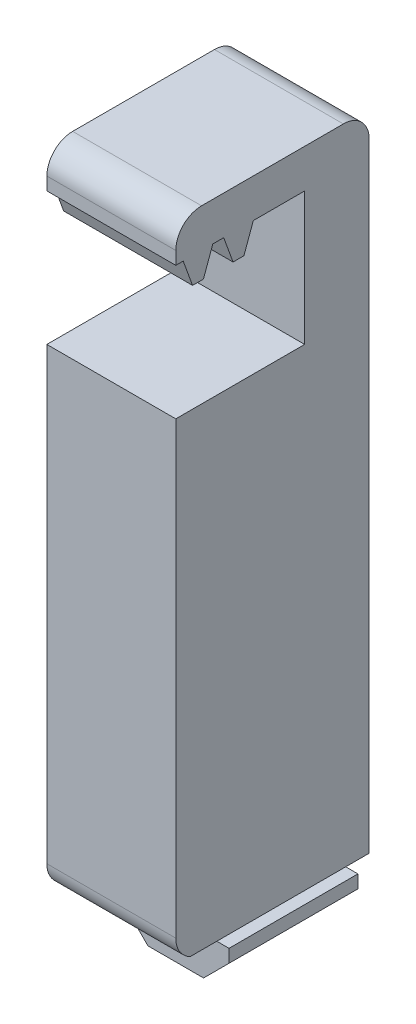
SolidWorks part; units mm, degrees
material "PLA Grey"
ref_plane "Front Plane" through (0, 0, 0) normal (0, 0, 1) x (1, 0, 0)
ref_plane "Top Plane" through (0, 0, 0) normal (0, 1, 0) x (1, 0, 0)
ref_plane "Right Plane" through (0, 0, 0) normal (1, 0, 0) x (0, 0, -1)
sketch "Sketch1" plane through (0, 0, 0) normal (1, 0, 0) x (0, 0, -1)
  line L0 (6.35, 0) -> (6.35, -6.096)
  line L1 (0, 63.7545) -> (12.7, 63.7545)
  line L2 (0, 63.7545) -> (0, 57.4045)
  line L3 (0, 57.4045) -> (12.7, 57.4045)
  line L5 (12.7, 63.7545) -> (19.05, 63.7545)
  line L6 (12.7, 57.4045) -> (12.7, 47.2445)
  line L7 (6.35, -6.096) -> (19.05, -6.096)
  line L8 (19.05, 63.7545) -> (19.05, -6.096)
  line L9 (12.7, 47.2445) -> (0, 47.2445)
  line L11 (6.35, 0) -> (0, 0)
  line L12 (0, 47.2445) -> (0, 0)
  line L13 (12.7, 47.2445) -> (-1206.5, 47.2445) construction
  line L14 (12.7, 47.2445) -> (-1206.5, 47.2445) construction
  point P14 (19.05, 45.72)
  dimension "D1" = 6.35
  dimension "D2" = 12.7
  dimension "D3" = 10.16
  dimension "D4" = 6.35
  dimension "D5" = 12.7
  dimension "D6" = 6.096
extrude "Boss-Extrude1" add sketch "Sketch1" along normal mid plane 12.7
sketch "Sketch2" plane through (6.35, 0, 0) normal (1, 0, 0) x (0, 0, -1)
  line L23 (7.6397, 59.9445) -> (8.7102, 59.9445) construction
  line L24 (7.6397, 59.9445) -> (6.6653, 57.2672) construction
  line L25 (-0.3399, 59.9445) -> (0.7305, 59.9445) construction
  line L26 (1.705, 57.2672) -> (0.7305, 59.9445) construction
  line L27 (2.4362, 57.0997) -> (1.9442, 57.0997) construction
  line L28 (3.6499, 59.9445) -> (2.6754, 57.2672) construction
  line L29 (3.6499, 59.9445) -> (4.7203, 59.9445) construction
  line L30 (5.6948, 57.2672) -> (4.7203, 59.9445) construction
  line L31 (6.4261, 57.0997) -> (5.934, 57.0997) construction
  line L32 (7.6397, 59.9445) -> (8.7102, 59.9445)
  line L33 (7.6397, 59.9445) -> (6.6653, 57.2672)
  line L34 (-0.3399, 59.9445) -> (0.7305, 59.9445)
  line L35 (1.705, 57.2672) -> (0.7305, 59.9445)
  line L36 (2.4362, 57.0997) -> (1.9442, 57.0997)
  line L37 (3.6499, 59.9445) -> (2.6754, 57.2672)
  line L38 (3.6499, 59.9445) -> (4.7203, 59.9445)
  line L39 (5.6948, 57.2672) -> (4.7203, 59.9445)
  line L40 (6.4261, 57.0997) -> (5.934, 57.0997)
  line L41 (8.7102, 59.9445) -> (12.7, 59.9445)
  line L42 (12.7, 59.9445) -> (12.7, 47.2445)
  line L43 (12.7, 57.4045) -> (12.7, 47.2445) construction
  line L44 (12.7, 47.2445) -> (0, 47.2445)
  line L45 (0, 47.2445) -> (0, 59.9445)
  line L46 (0, 63.7545) -> (0, 57.4045) construction
  line L47 (12.7, 47.2445) -> (-1206.5, 47.2445) construction
  arc A8 (6.4261, 57.0997) -> (6.6653, 57.2672) centre (6.4261, 57.3543) ccw construction
  arc A9 (1.705, 57.2672) -> (1.9442, 57.0997) centre (1.9442, 57.3543) ccw construction
  arc A10 (2.4362, 57.0997) -> (2.6754, 57.2672) centre (2.4362, 57.3543) ccw construction
  arc A11 (5.6948, 57.2672) -> (5.934, 57.0997) centre (5.934, 57.3543) ccw construction
  arc A12 (6.4261, 57.0997) -> (6.6653, 57.2672) centre (6.4261, 57.3543) ccw
  arc A13 (1.705, 57.2672) -> (1.9442, 57.0997) centre (1.9442, 57.3543) ccw
  arc A14 (2.4362, 57.0997) -> (2.6754, 57.2672) centre (2.4362, 57.3543) ccw
  arc A15 (5.6948, 57.2672) -> (5.934, 57.0997) centre (5.934, 57.3543) ccw
  line M17 (0, 63.7545) -> (0, 57.4045)
  line M18 (0, 57.4045) -> (12.7, 57.4045)
  line M19 (12.7, 57.4045) -> (12.7, 47.2445)
  line M20 (12.7, 47.2445) -> (0, 47.2445)
extrude "Cut-Extrude1" cut sketch "Sketch2" against normal through all contours A15 L39 L37 A14 L36 A13 L35 L45 L33 A12 L40 M18 M20 M19 | L39 L38 L37 M18 | L35 L34 M18 M17 | L42 L41 L32 L33 M18
sketch "Sketch3" plane through (0, 0, -19.05) normal (0, 0, -1) x (-1, 0, 0)
  line L0 (-6.35, -6.096) -> (-2.8393, -6.1)
  line L13 (2.8393, -6.1) -> (6.35, -6.096)
  line L15 (2.8393, -6.1) -> (5.5, -3.4393)
  line L16 (5.5, -3.4393) -> (5.5, -1.8)
  line L17 (5.5, -1.8) -> (3.125, -1.8)
  line L18 (3.125, -1.8) -> (3.125, -1.455)
  line L19 (3.125, -1.455) -> (4.58, 0)
  line L20 (15.42, 0) -> (4.58, 0)
  line L21 (-4.58, 0) -> (-9.5, 0)
  line L22 (-3.125, -1.455) -> (-4.58, 0)
  line L23 (-3.125, -1.8) -> (-3.125, -1.455)
  line L24 (-5.5, -1.8) -> (-3.125, -1.8)
  line L25 (-5.5, -3.4393) -> (-5.5, -1.8)
  line L26 (-2.8393, -6.1) -> (-5.5, -3.4393)
  line L29 (-9.5, 0) -> (-6.35, -6.096)
  line L32 (6.35, -6.096) -> (15.42, 0)
extrude "Cut-Extrude2" cut sketch "Sketch3" against normal through all
fillet "Fillet1" radius 2.54 3 edges at (0, 0, 0) (0, 63.7545, 0) (0, 63.7545, -19.05)
sketch "Sketch5" plane through (0, 0, -19.05) normal (0, 0, -1) x (-1, 0, 0)
  line L0 (6.35, 0) -> (4.58, 0) construction
  line L1 (4.58, 0) -> (3.125, -1.455) construction
  line L2 (3.125, -1.455) -> (3.125, -1.8) construction
  line L3 (3.125, -1.8) -> (5.5, -1.8) construction
  line L4 (5.5, -1.8) -> (5.5, -3.4393) construction
  line L5 (5.5, -3.4393) -> (2.8433, -6.096) construction
  line L6 (-2.8433, -6.096) -> (2.8433, -6.096) construction
  line L7 (-2.8433, -6.096) -> (-5.5, -3.4393) construction
  line L8 (-5.5, -3.4393) -> (-5.5, -1.8) construction
  line L9 (-5.5, -1.8) -> (-3.125, -1.8) construction
  line L10 (-3.125, -1.8) -> (-3.125, -1.455) construction
  line L11 (-3.125, -1.455) -> (-4.58, 0) construction
  line L12 (-4.58, 0) -> (-6.35, 0) construction
  line L13 (6.35, 0) -> (4.58, 0)
  line L14 (4.58, 0) -> (3.125, -1.455)
  line L15 (3.125, -1.455) -> (3.125, -1.8)
  line L16 (3.125, -1.8) -> (5.5, -1.8)
  line L17 (5.5, -1.8) -> (5.5, -3.4393)
  line L18 (5.5, -3.4393) -> (2.8433, -6.096)
  line L19 (-2.8433, -6.096) -> (2.8433, -6.096)
  line L20 (-2.8433, -6.096) -> (-5.5, -3.4393)
  line L21 (-5.5, -3.4393) -> (-5.5, -1.8)
  line L22 (-5.5, -1.8) -> (-3.125, -1.8)
  line L23 (-3.125, -1.8) -> (-3.125, -1.455)
  line L24 (-3.125, -1.455) -> (-4.58, 0)
  line L25 (-4.58, 0) -> (-6.35, 0)
  line L26 (6.35, 0.254) -> (4.4748, 0.254)
  line L27 (4.4748, 0.254) -> (2.871, -1.3498)
  line L28 (2.871, -1.3498) -> (2.871, -2.054)
  line L29 (2.871, -2.054) -> (5.246, -2.054)
  line L30 (5.246, -2.054) -> (5.246, -3.3341)
  line L31 (5.246, -3.3341) -> (2.7381, -5.842)
  line L32 (-2.7381, -5.842) -> (2.7381, -5.842)
  line L33 (-2.7381, -5.842) -> (-5.246, -3.3341)
  line L34 (-5.246, -3.3341) -> (-5.246, -2.054)
  line L35 (-5.246, -2.054) -> (-2.871, -2.054)
  line L36 (-2.871, -2.054) -> (-2.871, -1.3498)
  line L37 (-2.871, -1.3498) -> (-4.4748, 0.254)
  line L38 (-4.4748, 0.254) -> (-6.35, 0.254)
  line L39 (6.35, 0) -> (6.35, 0.254)
  line L40 (-6.35, 0) -> (-6.35, 0.254)
  dimension "D1" = 0.254
extrude "Cut-Extrude3" cut sketch "Sketch5" against normal through all
sketch "Sketch6" plane through (6.35, 0, 0) normal (1, 0, 0) x (0, 0, -1)
  line L0 (12.7, 59.9445) -> (12.7, 47.2445) construction
  line L1 (0, 47.2445) -> (12.7, 47.2445)
  line L2 (0, 47.2445) -> (0, 46.8476)
  line L3 (0, 46.8476) -> (12.7, 46.8476)
  line L4 (12.7, 47.2445) -> (12.7, 46.8476)
  dimension "D1" = 0.3969
extrude "Cut-Extrude4" cut sketch "Sketch6" against normal through all
sketch "Sketch7" [suppressed] plane through (6.35, 0, 0) normal (1, 0, 0) x (0, 0, -1)
  line L0 (19.05, 0.1984) -> (19.05, 42.926) construction
  line L1 (0, 28.8131) -> (19.05, 28.8131)
  line L2 (0, 28.8131) -> (0, 45.466)
  line L3 (0, 45.466) -> (19.05, 45.466)
  line L4 (19.05, 28.8131) -> (19.05, 45.466)
  line L5 (0, 28.8131) -> (19.05, 45.466) construction
  line L6 (0, 45.466) -> (19.05, 28.8131) construction
  line L7 (16.51, 45.466) -> (2.54, 45.466) construction
  point P4 (9.525, 37.1396)
extrude "Cut-Extrude5" [suppressed] cut sketch "Sketch7" against normal through all and the other way through all
